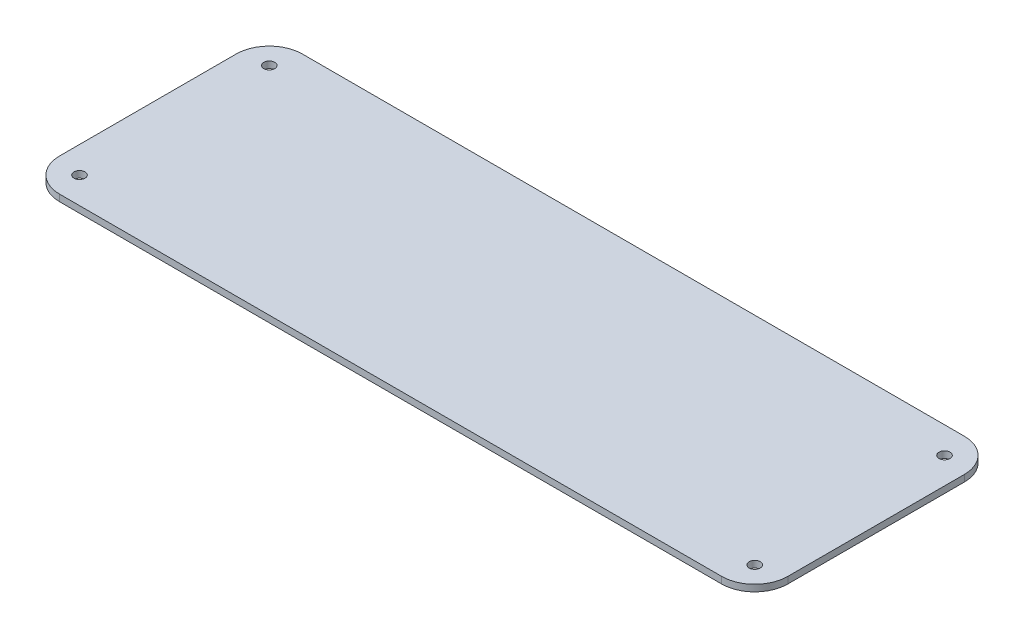
SolidWorks part; units mm, degrees
ref_plane "Plan de face" through (0, 0, 0) normal (0, 0, 1) x (1, 0, 0)
ref_plane "Plan de dessus" through (0, 0, 0) normal (0, 1, 0) x (1, 0, 0)
ref_plane "Plan de droite" through (0, 0, 0) normal (1, 0, 0) x (0, 0, -1)
sketch "Esquisse1" plane through (0, 0, 0) normal (0, 1, 0) x (1, 0, 0)
  line L0 (0, 98) -> (330, 98) construction
  line L1 (0, 0) -> (330, 0)
  line L2 (0, 0) -> (0, 110)
  line L3 (0, 110) -> (330, 110)
  line L4 (330, 0) -> (330, 110)
  line L5 (0, 55) -> (330, 55) construction
  line L6 (165, 110) -> (165, 0) construction
  line L7 (12, 110) -> (12, 0) construction
  circle A0 centre (12, 98) radius 2.5
  circle A1 centre (318, 98) radius 2.5
  circle A2 centre (318, 12) radius 2.5
  circle A3 centre (12, 12) radius 2.5
  point P13 (12, 98)
  dimension "D3" = 5
  dimension "D1" = 330
  dimension "D2" = 110
  dimension "D4" = 12
  dimension "D5" = 12
extrude "Extrusion1" add sketch "Esquisse1" along normal blind 3
fillet "Congé2" radius 15 4 edges at (0, 1.5, -110) (0, 1.5, 0) (330, 1.5, -110) (330, 1.5, 0)
